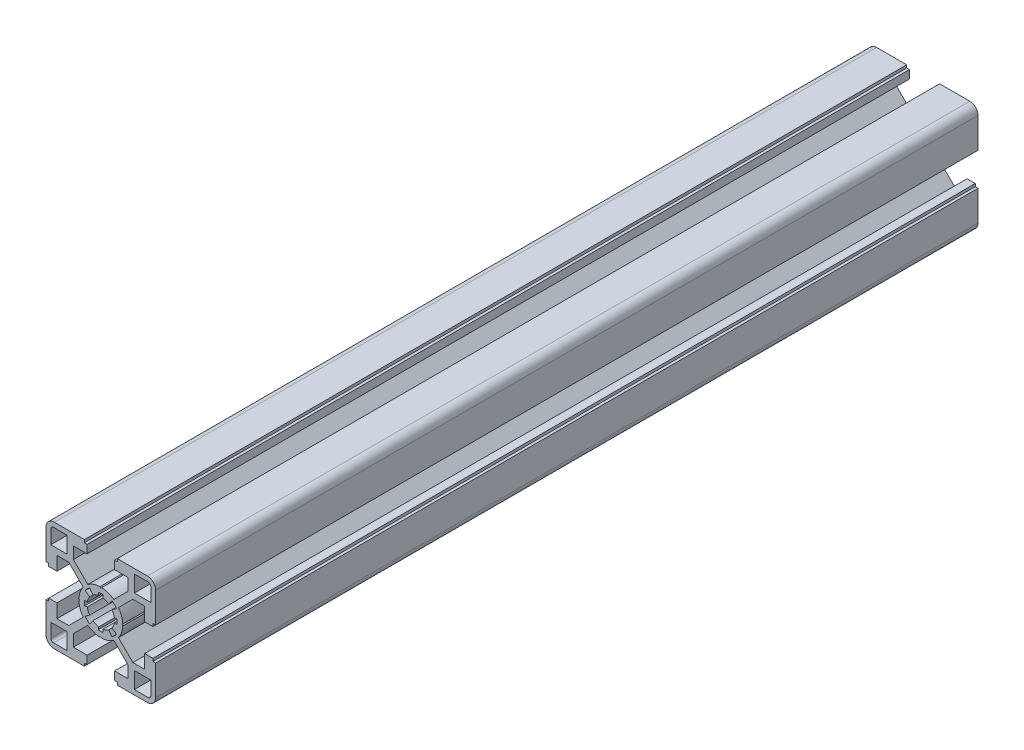
SolidWorks part; units mm, degrees
ref_plane "Plan de face" through (0, 0, 0) normal (0, 0, 1) x (1, 0, 0)
ref_plane "Plan de dessus" through (0, 0, 0) normal (0, 1, 0) x (1, 0, 0)
ref_plane "Plan de droite" through (0, 0, 0) normal (1, 0, 0) x (0, 0, -1)
ref_plane "Plan1" through (0, 0, 100) normal (0, 0, 1) x (1, 0, 0)
sketch "Esquisse1" plane through (0, 0, 100) normal (0, 0, 1) x (1, 0, 0)
  line L0 (18.25, 12.25) -> (12.25, 12.25)
  line L1 (12.25, 12.25) -> (12.25, 18.25)
  line L2 (12.25, 18.25) -> (17.25, 18.25)
  line L3 (18.25, 17.25) -> (18.25, 12.25)
  line L4 (-18.25, -12.25) -> (-12.25, -12.25)
  line L5 (-12.25, -12.25) -> (-12.25, -18.25)
  line L6 (-12.25, -18.25) -> (-17.25, -18.25)
  line L7 (-18.25, -17.25) -> (-18.25, -12.25)
  line L8 (6, -19) -> (6, -20)
  line L9 (6, -20) -> (17, -20)
  line L10 (20, -17) -> (20, -6)
  line L11 (20, -6) -> (19, -6)
  line L12 (19, -6) -> (19, -5)
  line L13 (19, -5) -> (16, -5)
  line L14 (16, -5) -> (16, -10)
  line L15 (16, -10) -> (11.6971, -10)
  line L16 (11.6971, -10) -> (6.4414, -4.7443)
  line L17 (7.9941, -0.3064) -> (7.7, 0)
  line L18 (7.7, 0) -> (7.9941, 0.3064)
  line L19 (6.4414, 4.7443) -> (11.6971, 10)
  line L20 (11.6971, 10) -> (16, 10)
  line L21 (16, 10) -> (16, 5)
  line L22 (16, 5) -> (19, 5)
  line L23 (19, 5) -> (19, 6)
  line L24 (19, 6) -> (20, 6)
  line L25 (20, 6) -> (20, 17)
  line L26 (17, 20) -> (6, 20)
  line L27 (6, 20) -> (6, 19)
  line L28 (6, 19) -> (5, 19)
  line L29 (5, 19) -> (5, 16)
  line L30 (5, 16) -> (10, 16)
  line L31 (10, 16) -> (10, 11.6971)
  line L32 (10, 11.6971) -> (4.7443, 6.4414)
  line L33 (0.3064, 7.9941) -> (0, 7.7)
  line L34 (0, 7.7) -> (-0.3064, 7.9941)
  line L35 (-4.7443, 6.4414) -> (-10, 11.6971)
  line L36 (-10, 11.6971) -> (-10, 16)
  line L37 (-10, 16) -> (-5, 16)
  line L38 (-5, 16) -> (-5, 19)
  line L39 (-5, 19) -> (-6, 19)
  line L40 (-6, 19) -> (-6, 20)
  line L41 (-6, 20) -> (-17, 20)
  line L42 (-20, 17) -> (-20, 6)
  line L43 (-20, 6) -> (-19, 6)
  line L44 (-19, 6) -> (-19, 5)
  line L45 (-19, 5) -> (-16, 5)
  line L46 (-16, 5) -> (-16, 10)
  line L47 (-16, 10) -> (-11.6971, 10)
  line L48 (-11.6971, 10) -> (-6.4414, 4.7443)
  line L49 (-7.9941, 0.3064) -> (-7.7, 0)
  line L50 (-7.7, 0) -> (-7.9941, -0.3064)
  line L51 (-6.4414, -4.7443) -> (-11.6971, -10)
  line L52 (-11.6971, -10) -> (-16, -10)
  line L53 (-16, -10) -> (-16, -5)
  line L54 (-16, -5) -> (-19, -5)
  line L55 (-19, -5) -> (-19, -6)
  line L56 (-19, -6) -> (-20, -6)
  line L57 (-20, -6) -> (-20, -17)
  line L58 (-17, -20) -> (-6, -20)
  line L59 (-6, -20) -> (-6, -19)
  line L60 (-6, -19) -> (-5, -19)
  line L61 (-5, -19) -> (-5, -16)
  line L62 (-5, -16) -> (-10, -16)
  line L63 (-10, -16) -> (-10, -11.6971)
  line L64 (-10, -11.6971) -> (-4.7443, -6.4414)
  line L65 (-0.3064, -7.9941) -> (0, -7.7)
  line L66 (0, -7.7) -> (0.3064, -7.9941)
  line L67 (4.7443, -6.4414) -> (10, -11.6971)
  line L68 (10, -11.6971) -> (10, -16)
  line L69 (10, -16) -> (5, -16)
  line L70 (5, -16) -> (5, -19)
  line L71 (5, -19) -> (6, -19)
  line L72 (-12.25, 18.25) -> (-12.25, 12.25)
  line L73 (-12.25, 12.25) -> (-18.25, 12.25)
  line L74 (-18.25, 12.25) -> (-18.25, 17.25)
  line L75 (-17.25, 18.25) -> (-12.25, 18.25)
  line L76 (12.25, -18.25) -> (12.25, -12.25)
  line L77 (12.25, -12.25) -> (18.25, -12.25)
  line L78 (18.25, -12.25) -> (18.25, -17.25)
  line L79 (17.25, -18.25) -> (12.25, -18.25)
  line L80 (-5.7057, -4.0552) -> (-4.0755, -2.8966)
  line L81 (-4.9435, -0.7494) -> (-5.9322, -0.8993)
  line L82 (-5.9322, 0.8993) -> (-4.9435, 0.7494)
  line L83 (-4.0755, 2.8966) -> (-5.7057, 4.0552)
  line L84 (-4.0641, 5.6994) -> (-2.903, 4.071)
  line L85 (-0.7494, 4.9435) -> (-0.8993, 5.9322)
  line L86 (0.8993, 5.9322) -> (0.7494, 4.9435)
  line L87 (2.903, 4.071) -> (4.0641, 5.6994)
  line L88 (5.7057, 4.0552) -> (4.0755, 2.8966)
  line L89 (4.9435, 0.7494) -> (5.9322, 0.8993)
  line L90 (5.9322, -0.8993) -> (4.9435, -0.7494)
  line L91 (4.0755, -2.8966) -> (5.7057, -4.0552)
  line L92 (4.0641, -5.6994) -> (2.903, -4.071)
  line L93 (0.7494, -4.9435) -> (0.8993, -5.9322)
  line L94 (-0.8993, -5.9322) -> (-0.7494, -4.9435)
  line L95 (-2.903, -4.071) -> (-4.0641, -5.6994)
  arc A0 (17.25, 18.25) -> (18.25, 17.25) centre (17.25, 17.25) cw
  arc A1 (-17.25, -18.25) -> (-18.25, -17.25) centre (-17.25, -17.25) cw
  arc A2 (17, -20) -> (20, -17) centre (17, -17) ccw
  arc A3 (6.4414, -4.7443) -> (7.9941, -0.3064) centre (0, 0) ccw
  arc A4 (7.9941, 0.3064) -> (6.4414, 4.7443) centre (0, 0) ccw
  arc A5 (20, 17) -> (17, 20) centre (17, 17) ccw
  arc A6 (4.7443, 6.4414) -> (0.3064, 7.9941) centre (0, 0) ccw
  arc A7 (-0.3064, 7.9941) -> (-4.7443, 6.4414) centre (0, 0) ccw
  arc A8 (-17, 20) -> (-20, 17) centre (-17, 17) ccw
  arc A9 (-6.4414, 4.7443) -> (-7.9941, 0.3064) centre (0, 0) ccw
  arc A10 (-7.9941, -0.3064) -> (-6.4414, -4.7443) centre (0, 0) ccw
  arc A11 (-20, -17) -> (-17, -20) centre (-17, -17) ccw
  arc A12 (-4.7443, -6.4414) -> (-0.3064, -7.9941) centre (0, 0) ccw
  arc A13 (0.3064, -7.9941) -> (4.7443, -6.4414) centre (0, 0) ccw
  arc A14 (-18.25, 17.25) -> (-17.25, 18.25) centre (-17.25, 17.25) cw
  arc A15 (18.25, -17.25) -> (17.25, -18.25) centre (17.25, -17.25) cw
  arc A16 (-4.0641, -5.6994) -> (-5.7057, -4.0552) centre (0, 0) cw
  arc A17 (-4.0755, -2.8966) -> (-4.9435, -0.7494) centre (0, 0) cw
  arc A18 (-5.9322, -0.8993) -> (-5.9322, 0.8993) centre (0, 0) cw
  arc A19 (-4.9435, 0.7494) -> (-4.0755, 2.8966) centre (0, 0) cw
  arc A20 (-5.7057, 4.0552) -> (-4.0641, 5.6994) centre (0, 0) cw
  arc A21 (-2.903, 4.071) -> (-0.7494, 4.9435) centre (0, 0) cw
  arc A22 (-0.8993, 5.9322) -> (0.8993, 5.9322) centre (0, 0) cw
  arc A23 (0.7494, 4.9435) -> (2.903, 4.071) centre (0, 0) cw
  arc A24 (4.0641, 5.6994) -> (5.7057, 4.0552) centre (0, 0) cw
  arc A25 (4.0755, 2.8966) -> (4.9435, 0.7494) centre (0, 0) cw
  arc A26 (5.9322, 0.8993) -> (5.9322, -0.8993) centre (0, 0) cw
  arc A27 (4.9435, -0.7494) -> (4.0755, -2.8966) centre (0, 0) cw
  arc A28 (5.7057, -4.0552) -> (4.0641, -5.6994) centre (0, 0) cw
  arc A29 (2.903, -4.071) -> (0.7494, -4.9435) centre (0, 0) cw
  arc A30 (0.8993, -5.9322) -> (-0.8993, -5.9322) centre (0, 0) cw
  arc A31 (-0.7494, -4.9435) -> (-2.903, -4.071) centre (0, 0) cw
extrude "Boss.-Extru.1" add sketch "Esquisse1" against normal blind 300
